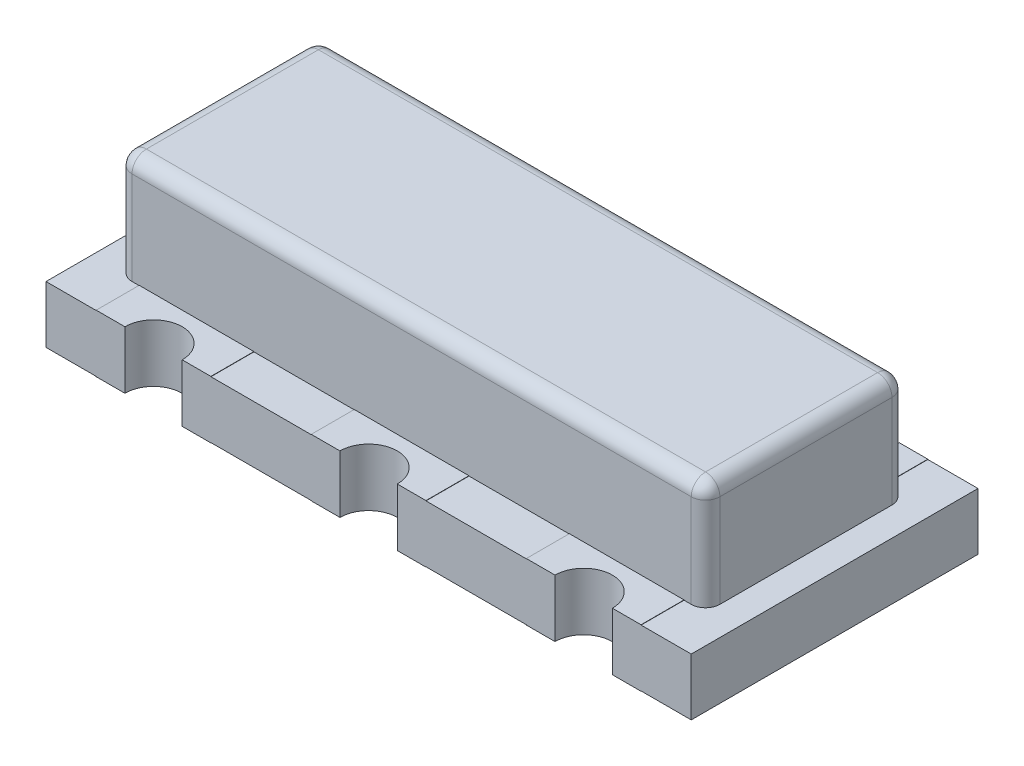
SolidWorks part; units mm, degrees
ref_plane "Front" through (0, 0, 0) normal (0, 0, 1) x (1, 0, 0)
ref_plane "Top" through (0, 0, 0) normal (0, 1, 0) x (1, 0, 0)
ref_plane "Right" through (0, 0, 0) normal (1, 0, 0) x (0, 0, -1)
sketch "Sketch1" plane through (0, 0, 0) normal (0, 1, 0) x (1, 0, 0)
  line L0 (0, -3.9631) -> (0, 3.342) construction
  line L1 (-6.0327, 0) -> (4.9033, 0) construction
  line L2 (1.7, -1) -> (2.25, -1)
  line L3 (-2.25, 1) -> (-1.7, 1)
  line L4 (-2.25, 1) -> (-2.25, -1)
  line L5 (-2.25, -1) -> (-1.7, -1)
  line L6 (2.25, 1) -> (2.25, -1)
  line L7 (0.2, -1) -> (1.3, -1)
  line L8 (-1.3, -1) -> (-0.2, -1)
  line L9 (-1.3, 1) -> (-0.2, 1)
  line L10 (0.2, 1) -> (1.3, 1)
  line L11 (1.7, 1) -> (2.25, 1)
  arc A0 (-1.7, 1) -> (-1.3, 1) centre (-1.5, 1) ccw
  arc A1 (-0.2, 1) -> (0.2, 1) centre (0, 1) ccw
  arc A2 (1.3, 1) -> (1.7, 1) centre (1.5, 1) ccw
  arc A3 (1.3, -1) -> (1.7, -1) centre (1.5, -1) cw
  arc A4 (-0.2, -1) -> (0.2, -1) centre (0, -1) cw
  arc A5 (-1.7, -1) -> (-1.3, -1) centre (-1.5, -1) cw
  dimension "D1" = 2
  dimension "D2" = 4.5
  dimension "D3" = 1.5
  dimension "D4" = 1.5
  dimension "D5" = 0.4
extrude "Extrude1" add sketch "Sketch1" along normal blind 0.398 from offset 0.002
sketch "Sketch2" plane through (0, 0, 0) normal (0, 1, 0) x (1, 0, 0)
  line L0 (-2.25, -1) -> (-1.7, -1) construction
  line L1 (-1.9, -1) -> (-1.7, -1)
  line L2 (-1.9, -1) -> (-1.9, -0.7)
  line L3 (-1.9, -0.7) -> (-1.7, -0.7)
  line L4 (-1.1, -1) -> (-1.1, -0.7)
  line L5 (-1.3, -1) -> (-0.2, -1) construction
  line L6 (-0.4, -1) -> (-0.2, -1)
  line L7 (-0.4, -1) -> (-0.4, -0.7)
  line L8 (-0.4, -0.7) -> (-0.2, -0.7)
  line L9 (0.4, -1) -> (0.4, -0.7)
  line L10 (0.2, -1) -> (1.3, -1) construction
  line L11 (1.1, -1) -> (1.3, -1)
  line L12 (1.1, -1) -> (1.1, -0.7)
  line L13 (1.1, -0.7) -> (1.3, -0.7)
  line L14 (1.9, -1) -> (1.9, -0.7)
  line L15 (-2.4433, 0) -> (2.422, 0) construction
  line L16 (1.7, -1) -> (1.9, -1)
  line L17 (0.2, -1) -> (0.4, -1)
  line L18 (-1.3, -1) -> (-1.1, -1)
  line L19 (0.2, -0.7) -> (0.2, 0.7)
  line L20 (-0.2, -0.7) -> (-0.2, 0.7)
  line L21 (1.3, -0.7) -> (1.3, 0.7)
  line L22 (1.7, -0.7) -> (1.7, 0.7)
  line L23 (-1.3, -0.7) -> (-1.3, 0.7)
  line L24 (-1.7, -0.7) -> (-1.7, 0.7)
  line L25 (1.7, -0.7) -> (1.9, -0.7)
  line L26 (0.2, -0.7) -> (0.4, -0.7)
  line L27 (-1.3, -0.7) -> (-1.1, -0.7)
  line L28 (0, 1.7234) -> (0, -1.9858) construction
  line L30 (-1.3, 0.7) -> (-1.1, 0.7)
  line L31 (0.2, 0.7) -> (0.4, 0.7)
  line L32 (-1.3, 1) -> (-1.1, 1)
  line L33 (0.2, 1) -> (0.4, 1)
  line L34 (1.7, 1) -> (1.9, 1)
  line L35 (1.1, 0.7) -> (1.3, 0.7)
  line L36 (1.1, 1) -> (1.1, 0.7)
  line L37 (1.1, 1) -> (1.3, 1)
  line L38 (0.4, 1) -> (0.4, 0.7)
  line L39 (-0.4, 0.7) -> (-0.2, 0.7)
  line L40 (-0.4, 1) -> (-0.4, 0.7)
  line L41 (-0.4, 1) -> (-0.2, 1)
  line L42 (-1.1, 1) -> (-1.1, 0.7)
  line L43 (-1.9, 0.7) -> (-1.7, 0.7)
  line L44 (-1.9, 1) -> (-1.9, 0.7)
  line L45 (-1.9, 1) -> (-1.7, 1)
  line L46 (1.9, 1) -> (1.9, 0.7)
  line L47 (1.7, 0.7) -> (1.9, 0.7)
  arc A0 (1.3, -1) -> (1.7, -1) centre (1.5, -1) cw
  arc A1 (-0.2, -1) -> (0.2, -1) centre (0, -1) cw
  arc A2 (-1.7, -1) -> (-1.3, -1) centre (-1.5, -1) cw
  arc A3 (1.7, -1) -> (1.3, -1) centre (1.5, -1) ccw construction
  arc A4 (0.2, -1) -> (-0.2, -1) centre (0, -1) ccw construction
  arc A5 (-1.3, -1) -> (-1.7, -1) centre (-1.5, -1) ccw construction
  arc A6 (-1.7, 1) -> (-1.3, 1) centre (-1.5, 1) ccw
  arc A7 (-0.2, 1) -> (0.2, 1) centre (0, 1) ccw
  arc A8 (1.3, 1) -> (1.7, 1) centre (1.5, 1) ccw
  dimension "D1" = 0.3
  dimension "D2" = 0.8
  dimension "D3" = 1.1
  dimension "D4" = 0.8
extrude "Extrude2" add sketch "Sketch2" along normal up to next
sketch "Sketch3" plane through (0, 0.4, 0) normal (0, 1, 0) x (1, 0, 0)
  line L1 (-1.9, -1) -> (-1.7, -1)
  line L2 (-1.9, -1) -> (-1.9, -0.7)
  line L3 (-1.9, -0.7) -> (-1.1, -0.7)
  line L4 (-1.1, -1) -> (-1.1, -0.7)
  line L5 (-0.2, 1) -> (-1.3, 1) construction
  line L6 (-0.4, -1) -> (-0.2, -1)
  line L7 (-0.4, -1) -> (-0.4, -0.7)
  line L8 (-1.7, 1) -> (-2.25, 1) construction
  line L9 (0.4, -1) -> (0.4, -0.7)
  line L10 (1.3, 1) -> (0.2, 1) construction
  line L11 (1.1, -1) -> (1.3, -1)
  line L12 (1.1, -1) -> (1.1, -0.7)
  line L13 (1.1, -0.7) -> (1.9, -0.7)
  line L14 (1.9, -1) -> (1.9, -0.7)
  line L15 (-2.4433, 0) -> (2.422, 0) construction
  line L16 (1.7, -1) -> (1.9, -1)
  line L17 (0.2, -1) -> (0.4, -1)
  line L18 (-1.3, -1) -> (-1.1, -1)
  line L26 (-0.4, -0.7) -> (0.4, -0.7)
  line L28 (0, 1.7234) -> (0, -1.9858) construction
  line L32 (-1.3, 1) -> (-1.1, 1)
  line L33 (0.2, 1) -> (0.4, 1)
  line L34 (1.7, 1) -> (1.9, 1)
  line L35 (1.1, 0.7) -> (1.9, 0.7)
  line L36 (1.1, 1) -> (1.1, 0.7)
  line L37 (1.1, 1) -> (1.3, 1)
  line L38 (0.4, 1) -> (0.4, 0.7)
  line L39 (-0.4, 0.7) -> (0.4, 0.7)
  line L40 (-0.4, 1) -> (-0.4, 0.7)
  line L41 (-0.4, 1) -> (-0.2, 1)
  line L42 (-1.1, 1) -> (-1.1, 0.7)
  line L43 (-1.9, 0.7) -> (-1.1, 0.7)
  line L44 (-1.9, 1) -> (-1.9, 0.7)
  line L45 (-1.9, 1) -> (-1.7, 1)
  line L46 (1.9, 1) -> (1.9, 0.7)
  arc A0 (1.3, -1) -> (1.7, -1) centre (1.5, -1) cw
  arc A1 (-0.2, -1) -> (0.2, -1) centre (0, -1) cw
  arc A2 (-1.7, -1) -> (-1.3, -1) centre (-1.5, -1) cw
  arc A6 (-1.7, 1) -> (-1.3, 1) centre (-1.5, 1) ccw
  arc A7 (-0.2, 1) -> (0.2, 1) centre (0, 1) ccw
  arc A8 (1.3, 1) -> (1.7, 1) centre (1.5, 1) ccw
  dimension "D6" = 0.2
  dimension "D1" = 0.3
  dimension "D2" = 1.1
  dimension "D3" = 0.3
  dimension "D4" = 0.8
  dimension "D5" = 1.5
extrude "Extrude3" add sketch "Sketch3" along normal blind 0.002
sketch "Sketch4" plane through (0, 0.4, 0) normal (0, 1, 0) x (1, 0, 0)
  line L0 (-1.9, 0.7) -> (-1.1, 0.7) construction
  line L1 (-2.05, 0.7) -> (2.05, 0.7)
  line L2 (-2.05, 0.7) -> (-2.05, -0.7)
  line L3 (-2.05, -0.7) -> (2.05, -0.7)
  line L4 (2.05, 0.7) -> (2.05, -0.7)
  line L5 (-1.1, -0.7) -> (-1.9, -0.7) construction
  line L6 (0, -1.5965) -> (0, 1.8104) construction
  dimension "D1" = 4.1
extrude "Extrude4" add sketch "Sketch4" along normal blind 0.75
fillet "Fillet1" radius 0.1 8 edges at (0, 1.15, -0.7) (-2.05, 1.15, 0) (0, 1.15, 0.7) (2.05, 1.15, 0) (-2.05, 0.775, -0.7) (2.05, 0.775, -0.7) (2.05, 0.775, 0.7) (-2.05, 0.775, 0.7)
